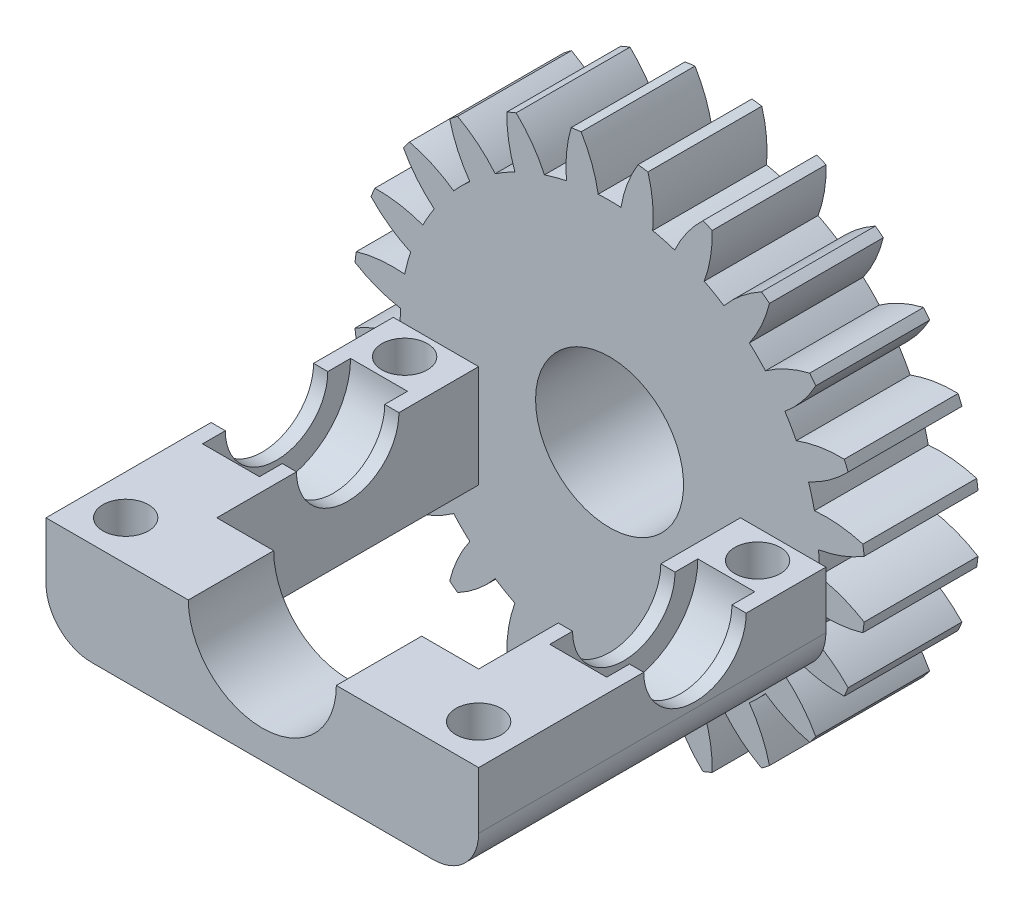
SolidWorks part; units mm, degrees
ref_plane "Front Plane" through (0, 0, 0) normal (0, 0, 1) x (1, 0, 0)
ref_plane "Top Plane" through (0, 0, 0) normal (0, 1, 0) x (1, 0, 0)
ref_plane "Right Plane" through (0, 0, 0) normal (1, 0, 0) x (0, 0, -1)
sketch "Sketch1" plane through (0, 0, 0) normal (0, 1, 0) x (1, 0, 0)
  line L2 (-19, 11.5) -> (-19, -19)
  line L3 (-19, -19) -> (19, -19)
  line L4 (19, 11.5) -> (19, -19)
  line L5 (-11.5, 11.5) -> (19, -19) construction
  line L6 (-19, -19) -> (11.5, 11.5) construction
  line L8 (-11.5, 11.5) -> (-11.5, -11.5)
  line L9 (-11.5, -11.5) -> (11.5, -11.5)
  line L10 (11.5, 11.5) -> (11.5, -11.5)
  line L11 (-11.5, 11.5) -> (11.5, -11.5) construction
  line L12 (-11.5, -11.5) -> (11.5, 11.5) construction
  line L13 (11.5, 11.5) -> (19, 11.5)
  line L14 (-11.5, 11.5) -> (-19, 11.5)
  point P0 (0, 0)
  point P6 (3.75, -3.75)
  dimension "D1" = 38
  dimension "D4" = 23
extrude "Boss-Extrude1" add sketch "Sketch1" along normal blind 9
ref_plane "Plane1" through (15.25, 0, 0) normal (1, 0, 0) x (0, 0, -1)
sketch "Sketch2" plane through (15.25, 0, 0) normal (1, 0, 0) x (0, 0, -1)
  line L1 (-19, 9) -> (-19, 0) construction
  circle A0 centre (0, 9) radius 6.5
  dimension "D1" = 13
  dimension "D2" = 19
extrude "Cut-Extrude1" cut sketch "Sketch2" against normal blind 2.5 and the other way blind 2.5
sketch "Sketch3" plane through (0, 0, 0) normal (1, 0, 0) x (0, 0, -1)
  line L1 (0, 9) -> (0, 0) construction
  circle A0 centre (0, 9) radius 4.5
  dimension "D1" = 9
extrude "Cut-Extrude2" cut sketch "Sketch3" along normal through all
mirror "Mirror1" about plane through (0, 0, 0) normal (1, 0, 0) of "Cut-Extrude1", "Cut-Extrude2"
sketch "Sketch5" plane through (0, 0, -11.5) normal (0, 0, -1) x (-1, 0, 0)
  line L0 (0, 0) -> (0, 9) construction
  circle A0 centre (0, 9) radius 22.5
  dimension "D1" = 45
  dimension "D2" = 9
extrude "Boss-Extrude2" add sketch "Sketch5" along normal blind 10
fillet "Fillet1" radius 4 2 edges at (-19, 0, 3.75) (19, 0, 3.75)
sketch "Sketch4" plane through (0, 0, 0) normal (0, 0, 1) x (1, 0, 0)
  line L0 (-19, 9) -> (19, 9) construction
  circle A0 centre (0, 9) radius 6.5
  dimension "D1" = 13
extrude "Cut-Extrude3" cut sketch "Sketch4" along normal through all both and the other way through all
sketch "Sketch6" plane through (0, 9, 0) normal (0, 1, 0) x (1, 0, 0)
  line L0 (-15.5, 9) -> (15.5, 9) construction
  line L1 (15.5, 9) -> (15.5, -15.5) construction
  line L2 (15.5, -15.5) -> (-15.5, -15.5) construction
  line L3 (-15.5, -15.5) -> (-15.5, 9) construction
  line L4 (-19, -4.5) -> (-19, -19) construction
  line L5 (-19, -19) -> (-6.5, -19) construction
  line L6 (19, -19) -> (19, -4.5) construction
  line L7 (-22.5, 11.5) -> (22.5, 11.5) construction
  circle A0 centre (-15.5, -15.5) radius 2
  circle A1 centre (15.5, -15.5) radius 2
  circle A2 centre (15.5, 9) radius 2
  circle A3 centre (-15.5, 9) radius 2
  dimension "D1" = 3.5
  dimension "D2" = 3.5
  dimension "D3" = 3.5
  dimension "D4" = 2.5
extrude "Cut-Extrude4" cut sketch "Sketch6" against normal through all
sketch "Sketch7" plane through (0, 0, -21.5) normal (0, 0, -1) x (-1, 0, 0)
  line L0 (-12.2364, 25.4283) -> (12.2364, 25.4283) construction
  line L1 (0, 31.3607) -> (0, 9) construction
  line L2 (-2.5, 31.3607) -> (2.5, 31.3607) construction
  arc A0 (-2.5, 31.3607) -> (-1, 27.3607) centre (-12.2364, 25.4283) cw
  circle A1 centre (0, 9) radius 22.5 construction
  arc A2 (2.5, 31.3607) -> (1, 27.3607) centre (12.2364, 25.4283) ccw
  arc A3 (-1, 27.3607) -> (1, 27.3607) centre (0, 9) cw
  arc A4 (-2.5, 31.3607) -> (2.5, 31.3607) centre (0, 9) cw
  point P13 (0, 25.4283)
  dimension "D1" = 2
  dimension "D2" = 4
  dimension "D3" = 5
extrude "Cut-Extrude5" cut sketch "Sketch7" against normal blind 10
pattern_circular "CirPattern1" count 24 every 15 about axis through (0, 9, 0) along (0, 0, 1) of "Cut-Extrude5"
